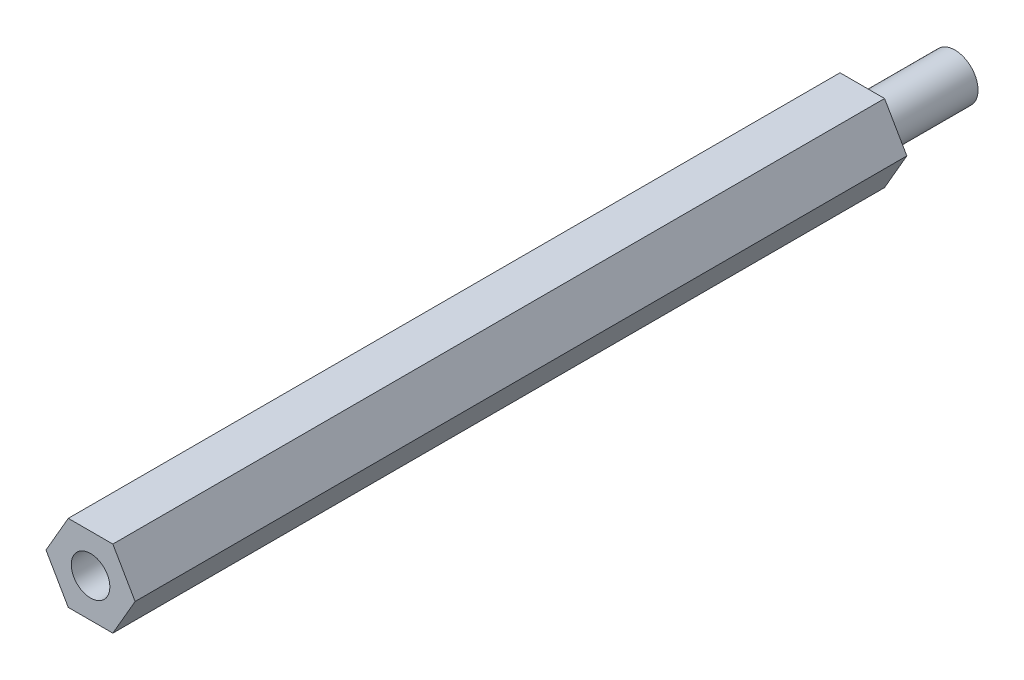
SolidWorks part; units mm, degrees
material "黃銅"
ref_plane "前基準面" through (0, 0, 0) normal (0, 0, 1) x (1, 0, 0)
ref_plane "上基準面" through (0, 0, 0) normal (0, 1, 0) x (1, 0, 0)
ref_plane "右基準面" through (0, 0, 0) normal (1, 0, 0) x (0, 0, -1)
sketch "草圖1" plane through (0, 0, 0) normal (0, 0, 1) x (1, 0, 0)
  line L1 (-1.4434, 2.5) -> (-2.8868, 0)
  line L2 (-2.8868, 0) -> (-1.4434, -2.5)
  line L3 (-1.4434, -2.5) -> (1.4434, -2.5)
  line L4 (1.4434, -2.5) -> (2.8868, 0)
  line L5 (2.8868, 0) -> (1.4434, 2.5)
  line L6 (1.4434, 2.5) -> (-1.4434, 2.5)
  circle A0 centre (0, 0) radius 2.5 construction
  dimension "D1" = 5
extrude "填料-伸長1" add sketch "草圖1" along normal blind 50
sketch "草圖4" plane through (0, 0, 0) normal (0, 0, -1) x (-1, 0, 0)
  circle A0 centre (0, 0) radius 1.5
  dimension "D1" = 3
extrude "填料-伸長2" add sketch "草圖4" along normal blind 6
hole_wizard "M3x0.5 螺紋孔1" positions "草圖2" profile "草圖3" tap size "M3x0.5" standard "Ansi Metric"
sketch "草圖2" plane through (0, 0, 50) normal (0, 0, 1) x (1, 0, 0)
  point P0 (0, 0)
sketch "草圖3" plane through (0, 0, 50) normal (1, 0, 0) x (0, -1, 0)
  line L0 (0, 0) -> (0, 8.2511)
  line L1 (0, 8.2511) -> (1.25, 7.5)
  line L2 (1.25, 7.5) -> (1.25, 0)
  line L5 (1.25, 0) -> (0, 0)
  line L10 (0, 8.2511) -> (-1.25, 7.5) construction
  line L11 (0, -6.35) -> (0, 107.95) construction
  dimension "螺孔鑽直徑" = 2.5
  dimension "螺孔鑽深度" = 7.5
  dimension "導頭角度" = 118
